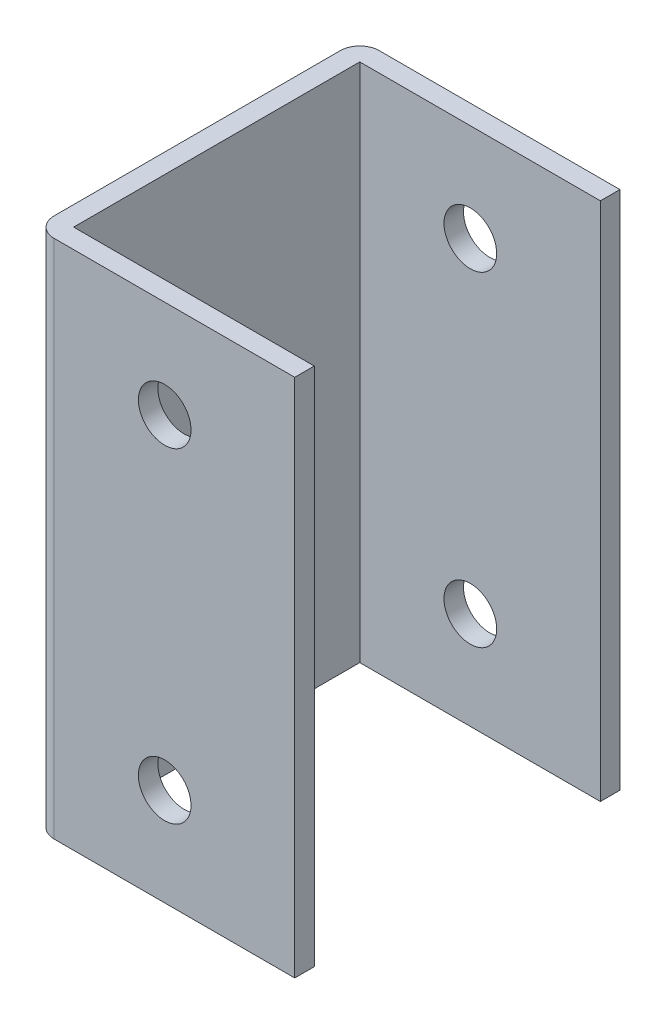
SolidWorks part; units mm, degrees
ref_plane "Спереди" through (0, 0, 0) normal (0, 0, 1) x (1, 0, 0)
ref_plane "Сверху" through (0, 0, 0) normal (0, 1, 0) x (1, 0, 0)
ref_plane "Справа" through (0, 0, 0) normal (1, 0, 0) x (0, 0, -1)
sketch "Эскиз1" plane through (0, 0, 0) normal (0, 1, 0) x (1, 0, 0)
  line L1 (-37, 25) -> (37, 25)
  line L2 (-40, 22) -> (-40, -22)
  line L3 (-37, -25) -> (37, -25)
  line L4 (40, 22) -> (40, -22)
  line L5 (-40, 25) -> (40, -25) construction
  line L6 (-40, -25) -> (40, 25) construction
  arc A0 (-37, 25) -> (-40, 22) centre (-37, 22) ccw
  arc A1 (-40, -22) -> (-37, -25) centre (-37, -22) ccw
  arc A2 (37, -25) -> (40, -22) centre (37, -22) ccw
  arc A3 (37, 25) -> (40, 22) centre (37, 22) cw
  point P0 (0, 0)
  dimension "D1" = 3
extrude "Вытянуть-Тонкостенный1" add sketch "Эскиз1" along normal blind 80 thin
sketch "Эскиз2" plane through (0, 80, 0) normal (0, 1, 0) x (1, 0, 0)
  line L1 (0, -27.4206) -> (41.1465, -27.4206)
  line L2 (0, -27.4206) -> (0, 30.9728)
  line L3 (0, 30.9728) -> (41.1465, 30.9728)
  line L4 (41.1465, -27.4206) -> (41.1465, 30.9728)
extrude "Вырез-Вытянуть1" cut sketch "Эскиз2" against normal through all
sketch "Эскиз3" plane through (0, 0, -25) normal (0, 0, -1) x (-1, 0, 0)
  circle A0 centre (20, 115) radius 4.05
  circle A1 centre (20, 15) radius 4.05
  circle A2 centre (20, 65) radius 4.05
  dimension "D1" = 2
  dimension "D2" = 2
extrude "Вырез-Вытянуть2" cut sketch "Эскиз3" against normal through all
